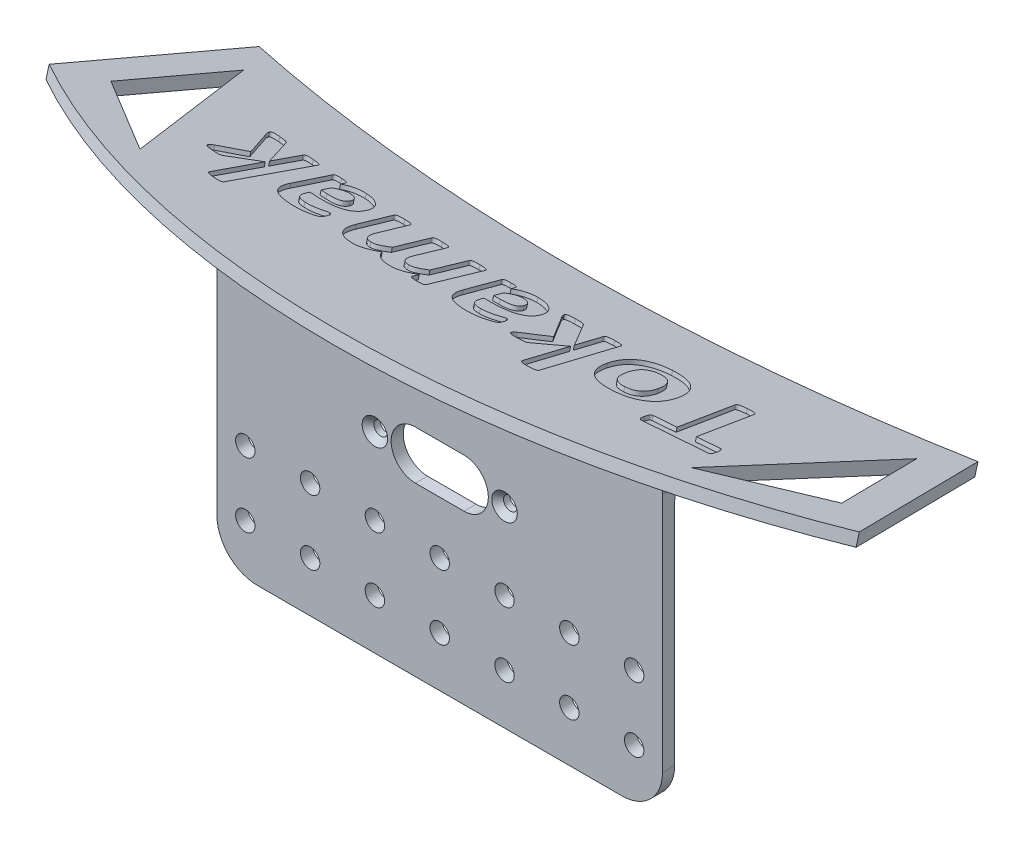
SolidWorks part; units mm, degrees
ref_plane "Front Plane" through (0, 0, 0) normal (0, 0, 1) x (1, 0, 0)
ref_plane "Top Plane" through (0, 0, 0) normal (0, 1, 0) x (1, 0, 0)
ref_plane "Right Plane" through (0, 0, 0) normal (1, 0, 0) x (0, 0, -1)
sketch "Sketch2" plane through (0, 0, 0) normal (0, 0, 1) x (1, 0, 0)
  line L1 (-55, -40) -> (55, -40)
  line L2 (-55, -40) -> (-55, 40)
  line L3 (-55, 40) -> (55, 40)
  line L4 (55, -40) -> (55, 40)
  line L5 (-55, -40) -> (55, 40) construction
  line L6 (-55, 40) -> (55, -40) construction
  point P0 (0, 0)
  dimension "D1" = 110
  dimension "D2" = 80
extrude "Boss-Extrude1" add sketch "Sketch2" along normal blind 3
ref_plane "Plane1" through (0, 36.5705, -9.799) normal (0, 0.9659, -0.2588) x (-1, 0, 0)
sketch "Sketch3" plane through (0, 36.5705, -9.799) normal (0, 0.9659, -0.2588) x (-1, 0, 0)
  line L0 (-100, 10.3528) -> (-88.7461, -31.6472)
  line L1 (100, 10.3528) -> (88.7461, -31.6472)
  line L2 (0, 0) -> (0, 50000) construction
  line L3 (-98.4411, 4.5347) -> (12842.5112, -48291.7566) construction
  line L4 (102.6283, 20.1618) -> (-12838.3239, -48276.1295) construction
  line L5 (-31.072, -19.6472) -> (49968.928, -19.6472) construction
  line L6 (-20.2868, 40.3528) -> (49979.7132, 40.3528) construction
  line L7 (-105.6954, 10.3528) -> (49894.3046, 10.3528) construction
  line L8 (-118.0145, -31.6472) -> (49881.9855, -31.6472) construction
  line L9 (-55, 10.3528) -> (55, 10.3528) construction
  arc A0 (-88.7461, -31.6472) -> (88.7461, -31.6472) centre (0, -353.8088) cw
  arc A1 (-100, 10.3528) -> (100, 10.3528) centre (0, -141.3139) cw
  dimension "D1" = 30
  dimension "D2" = 60
  dimension "D3" = 30
  dimension "D4" = 12
  dimension "D5" = 200
extrude "Boss-Extrude2" add sketch "Sketch3" along normal blind 3
fillet "Fillet1" radius 10 4 edges at (0, 39.1962, 0) (0, 40, 3) (55, 39.5981, 1.5) (-55, 39.5981, 1.5)
fillet "Fillet2" radius 10 2 edges at (55, -40, 1.5) (-55, -40, 1.5)
sketch "Sketch4" plane through (0, 0, 3) normal (0, 0, 1) x (1, 0, 0)
  circle A0 centre (-48, -11.6273) radius 2.4
  circle A1 centre (-48, -27.6273) radius 2.4
  circle A2 centre (-32, -11.6273) radius 2.4
  circle A3 centre (-32, -27.6273) radius 2.4
  circle A4 centre (-16, -11.6273) radius 2.4
  circle A5 centre (-16, -27.6273) radius 2.4
  circle A6 centre (0, -11.6273) radius 2.4
  circle A7 centre (0, -27.6273) radius 2.4
  circle A8 centre (16, -11.6273) radius 2.4
  circle A9 centre (16, -27.6273) radius 2.4
  circle A10 centre (32, -11.6273) radius 2.4
  circle A11 centre (32, -27.6273) radius 2.4
  circle A12 centre (48, -11.6273) radius 2.4
  circle A13 centre (48, -27.6273) radius 2.4
  circle A14 centre (48, -27.6273) radius 2.4 construction
  circle A15 centre (48, -11.6273) radius 2.4 construction
  circle A16 centre (32, -11.6273) radius 2.4 construction
  circle A17 centre (32, -27.6273) radius 2.4 construction
  circle A18 centre (16, -11.6273) radius 2.4 construction
  circle A19 centre (16, -27.6273) radius 2.4 construction
  circle A20 centre (0, -11.6273) radius 2.4 construction
  circle A21 centre (0, -27.6273) radius 2.4 construction
  circle A22 centre (-16, -11.6273) radius 2.4 construction
  circle A23 centre (-16, -27.6273) radius 2.4 construction
  circle A24 centre (-32, -11.6273) radius 2.4 construction
  circle A25 centre (-32, -27.6273) radius 2.4 construction
  circle A26 centre (-48, -11.6273) radius 2.4 construction
  circle A27 centre (-48, -27.6273) radius 2.4 construction
extrude "Cut-Extrude1" cut sketch "Sketch4" against normal through all
sketch "Sketch7" plane through (0, 39.4683, -10.5755) normal (0, 0.9659, -0.2588) x (1, 0, 0)
  line L0 (90.202, -4.6959) -> (83.0893, 21.8493)
  line L1 (83.0893, 21.8493) -> (68.0849, -20.1825)
  line L2 (68.0849, -20.1825) -> (90.202, -4.6959)
  line L3 (100, -10.3528) -> (88.7461, 31.6472) construction
  line L4 (106.1075, -8.7163) -> (-48190.1838, -12949.6685) construction
  line L5 (88.7461, 31.6472) -> (48385.0374, 12972.5995) construction
  dimension "D1" = 8
  dimension "D2" = 70
  dimension "D3" = 8
  dimension "D4" = 8
  dimension "D5" = 27
extrude "Cut-Extrude2" cut sketch "Sketch7" against normal through all
mirror "Mirror1" about plane through (0, 0, 0) normal (1, 0, 0) of "Cut-Extrude2"
sketch "Sketch8" plane through (0, 0, 3) normal (0, 0, 1) x (1, 0, 0)
  line L0 (-6, 7.3727) -> (6, 7.3727) construction
  line L1 (-6, 13.3727) -> (6, 13.3727)
  line L2 (-6, 1.3727) -> (6, 1.3727)
  line L3 (0, 0) -> (0, 50000) construction
  line L4 (50, 0.3727) -> (-50, 0.3727) construction
  line L5 (-10, 7.3727) -> (49990, 7.3727) construction
  arc A0 (-6, 13.3727) -> (-6, 1.3727) centre (-6, 7.3727) ccw
  arc A1 (6, 1.3727) -> (6, 13.3727) centre (6, 7.3727) ccw
  point P2 (0, 7.3727)
  dimension "D2" = 6
  dimension "D1" = 12
  dimension "D3" = 7
extrude "Cut-Extrude3" cut sketch "Sketch8" against normal through all
sketch "Sketch9" plane through (0, 39.4683, -10.5755) normal (0, 0.9659, -0.2588) x (-1, 0, 0)
  line L0 (-27.5265, -10) -> (49972.4735, -10) construction
  line L1 (0, 0) -> (0, 50000) construction
  line L2 (-13.6415, -4) -> (49986.3585, -4) construction
  arc A0 (-75, -10) -> (75, -10) centre (0, -475.75) cw construction
  text T0 "<b>Tokamak</b>" font "Calibri" height in points 80
  dimension "D3" = 6
  dimension "D1" = 10
  dimension "D2" = 150
extrude "Cut-Extrude11" cut sketch "Sketch9" against normal blind 1
hole_wizard "CSK for M3 Countersunk Flat Head Screw1" positions "Sketch11" profile "Sketch10" countersink size "M3" standard "ISO" end condition through all
sketch "Sketch11" plane through (0, 0, 3) normal (0, 0, 1) x (1, 0, 0)
  line L0 (-7.2451, 7.3727) -> (49992.7549, 7.3727) construction
  line L1 (6, 13.3727) -> (-6, 13.3727) construction
  line L2 (-6, 1.3727) -> (6, 1.3727) construction
  line L3 (0, 0) -> (0, 50000) construction
  point P0 (-16, 7.3727)
  point P2 (16, 7.3727)
  dimension "D1" = 32
sketch "Sketch10" plane through (-16, 7.3727, 3) normal (1, 0, 0) x (0, -1, 0)
  line L0 (0, 0) -> (0, 44.1444)
  line L1 (0, 44.1444) -> (1.7, 44.1444)
  line L2 (1.7, 44.1444) -> (1.7, 1.45)
  line L3 (1.7, 1.45) -> (3.15, 0)
  line L5 (3.15, 0) -> (0, 0)
  line L6 (-1.7, 1.45) -> (-3.15, 0) construction
  line L11 (0, -6.35) -> (0, 107.95) construction
  dimension "Thru Hole Dia." = 3.4
  dimension "Thru Hole Depth" = 44.1444
  dimension "Near C'Sink Dia." = 6.3
  dimension "Near C'Sink Angle" = 90
